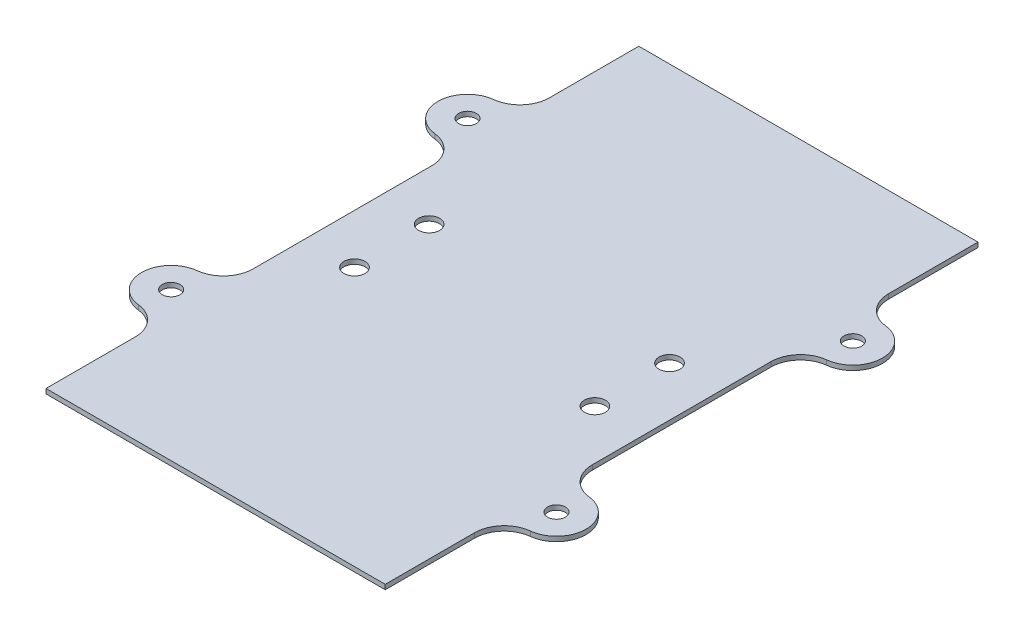
SolidWorks part; units mm, degrees
material "Acrylic (Medium-high impact)"
ref_plane "Front Plane" through (0, 0, 0) normal (0, 0, 1) x (1, 0, 0)
ref_plane "Top Plane" through (0, 0, 0) normal (0, 1, 0) x (1, 0, 0)
ref_plane "Right Plane" through (0, 0, 0) normal (1, 0, 0) x (0, 0, -1)
sketch "Sketch1" plane through (0, 0, 0) normal (0, 1, 0) x (1, 0, 0)
  line L0 (-73.7407, 62.9305) -> (-4.2407, 62.9305) construction
  line L1 (-75.3282, 62.9305) -> (-2.6532, 62.9305)
  line L2 (-75.3282, 62.9305) -> (-75.3282, -64.0695)
  line L3 (-75.3282, -64.0695) -> (-2.6532, -64.0695)
  line L4 (-2.6532, 62.9305) -> (-2.6532, -64.0695)
extrude "Boss-Extrude1" add sketch "Sketch1" along normal blind 1.016
sketch "Sketch2" plane through (0, 0, 0) normal (0, -1, 0) x (1, 0, 0)
  circle A0 centre (-64.7407, 8.5695) radius 2.25
  circle A1 centre (-64.7407, -7.4305) radius 2.25
  circle A2 centre (-13.2407, -7.4305) radius 2.25
  circle A3 centre (-13.2407, 8.5695) radius 2.25
  circle A4 centre (-64.7407, 8.5695) radius 2.25 construction
extrude "Cut-Extrude1" cut sketch "Sketch2" against normal through all
sketch "Sketch3" plane through (0, 1.016, 0) normal (0, 1, 0) x (1, 0, 0)
  line L0 (-80.2657, 37.5305) -> (-75.3282, 37.5305)
  line L1 (-75.3282, 62.9305) -> (-75.3282, -64.0695) construction
  line L2 (-80.2657, 24.8305) -> (-75.3282, 24.8305)
  line L3 (-75.3282, -0.5695) -> (-2.6532, -0.5695) construction
  line L4 (-2.6532, -64.0695) -> (-2.6532, 62.9305) construction
  line L5 (-38.9907, 62.9305) -> (-38.9907, -64.0695) construction
  line L6 (-2.6532, 62.9305) -> (-75.3282, 62.9305) construction
  line L7 (-75.3282, -64.0695) -> (-2.6532, -64.0695) construction
  line L8 (2.2843, 24.8305) -> (-2.6532, 24.8305)
  line L9 (2.2843, 37.5305) -> (-2.6532, 37.5305)
  line L10 (-75.3282, 37.5305) -> (-75.3282, 24.8305)
  line L11 (-2.6532, 37.5305) -> (-2.6532, 24.8305)
  line L12 (-75.3282, -38.6695) -> (-75.3282, -25.9695)
  line L13 (2.2843, -25.9695) -> (-2.6532, -25.9695)
  line L14 (-80.2657, -25.9695) -> (-75.3282, -25.9695)
  line L15 (2.2843, -38.6695) -> (-2.6532, -38.6695)
  line L16 (-80.2657, -38.6695) -> (-75.3282, -38.6695)
  line L17 (-2.6532, -38.6695) -> (-2.6532, -25.9695)
  arc A0 (-80.2657, 37.5305) -> (-80.2657, 24.8305) centre (-80.2657, 31.1805) ccw
  arc A1 (2.2843, 37.5305) -> (2.2843, 24.8305) centre (2.2843, 31.1805) cw
  arc A2 (2.2843, -38.6695) -> (2.2843, -25.9695) centre (2.2843, -32.3195) ccw
  arc A3 (-80.2657, -38.6695) -> (-80.2657, -25.9695) centre (-80.2657, -32.3195) cw
  dimension "D1" = 82.55
  dimension "D2" = 6.35
  dimension "D3" = 63.5
extrude "Boss-Extrude2" add sketch "Sketch3" against normal up to surface (1.016 mm away) up to face at (-13.2407, 0, 6.3195)
hole_wizard "#6 Clearance Hole1" positions "Sketch5" profile "Sketch4" hole size "#6" standard "ANSI Inch" end condition through all
sketch "Sketch5" plane through (0, 1.016, 0) normal (0, 1, 0) x (1, 0, 0)
  point P0 (-80.2657, 31.1805)
  point P3 (-80.2657, -32.3195)
  point P6 (2.2843, -32.3195)
  point P9 (2.2843, 31.1805)
sketch "Sketch4" plane through (-80.2657, 1.016, -31.1805) normal (1, 0, 0) x (0, 0, 1)
  line L0 (0, 0) -> (0, 1.016)
  line L1 (0, 1.016) -> (1.8986, 1.016)
  line L2 (1.8986, 1.016) -> (1.8986, 0)
  line L5 (1.8986, 0) -> (0, 0)
  line L11 (0, -6.35) -> (0, 107.95) construction
  dimension "Thru Hole Dia." = 3.7973
  dimension "Thru Hole Depth" = 1.016
fillet "Fillet1" radius 6.35 8 edges at (-75.3282, 0.508, 25.9695) (-75.3282, 0.508, 38.6695) (-2.6532, 0.508, 25.9695) (-2.6532, 0.508, 38.6695)
